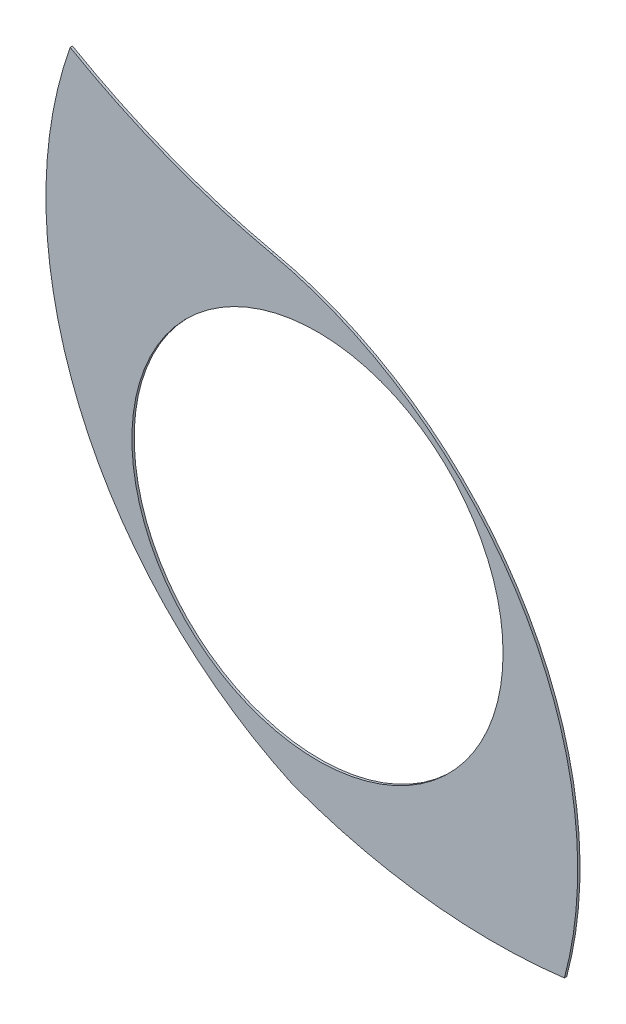
SolidWorks part; units mm, degrees
ref_plane "Alzado" through (0, 0, 0) normal (0, 0, 1) x (1, 0, 0)
ref_plane "Planta" through (0, 0, 0) normal (0, 1, 0) x (1, 0, 0)
ref_plane "Vista lateral" through (0, 0, 0) normal (1, 0, 0) x (0, 0, -1)
sketch "Model" plane through (0, 0, 0) normal (0, 0, 1) x (1, 0, 0)
  circle A0 centre (16.5014, 17.9949) radius 8
  arc A1 (27.1455, 7.1944) -> (14.524, 27.9267) centre (10.951, 11.5436) ccw
  arc A2 (5.8411, 31.2852) -> (14.524, 27.9267) centre (21.1065, 57.8481) ccw
  arc A3 (5.8411, 31.2852) -> (15.4238, 8.566) centre (23.1054, 25.1865) ccw
  arc A4 (15.4238, 8.566) -> (27.1455, 7.1944) centre (24.0995, 31.9359) ccw
extrude "Saliente-Extruir1" add sketch "Model" along normal blind 0.1
